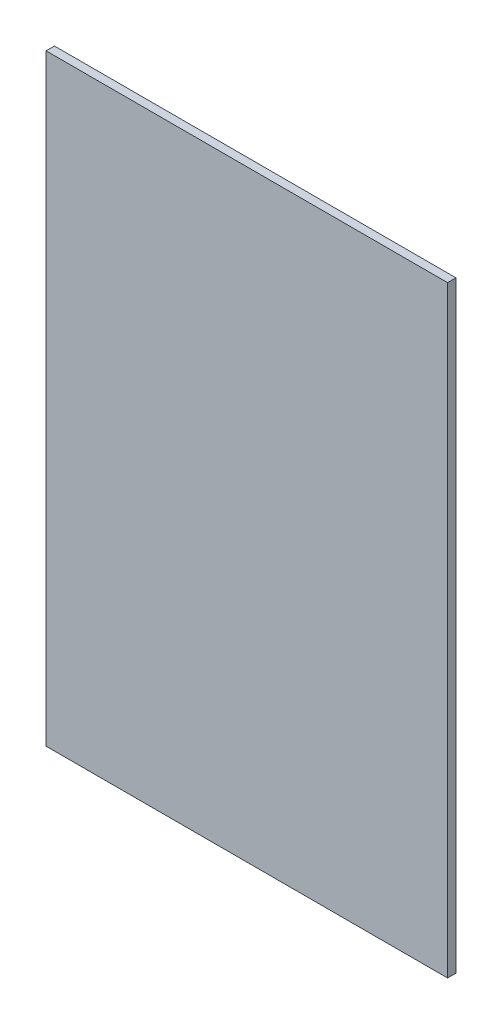
SolidWorks part; units mm, degrees
ref_plane "Front Plane" through (0, 0, 0) normal (0, 0, 1) x (1, 0, 0)
ref_plane "Top Plane" through (0, 0, 0) normal (0, 1, 0) x (1, 0, 0)
ref_plane "Right Plane" through (0, 0, 0) normal (1, 0, 0) x (0, 0, -1)
sketch "Sketch1" plane through (0, 0, 0) normal (0, 0, 1) x (1, 0, 0)
  line L1 (-304.8, -457.2) -> (304.8, -457.2)
  line L2 (-304.8, -457.2) -> (-304.8, 457.2)
  line L3 (-304.8, 457.2) -> (304.8, 457.2)
  line L4 (304.8, -457.2) -> (304.8, 457.2)
  line L5 (-304.8, -457.2) -> (304.8, 457.2) construction
  line L6 (-304.8, 457.2) -> (304.8, -457.2) construction
  point P0 (0, 0)
  dimension "D1" = 609.6
  dimension "D2" = 914.4
extrude "Boss-Extrude1" add sketch "Sketch1" along normal blind 12.7
